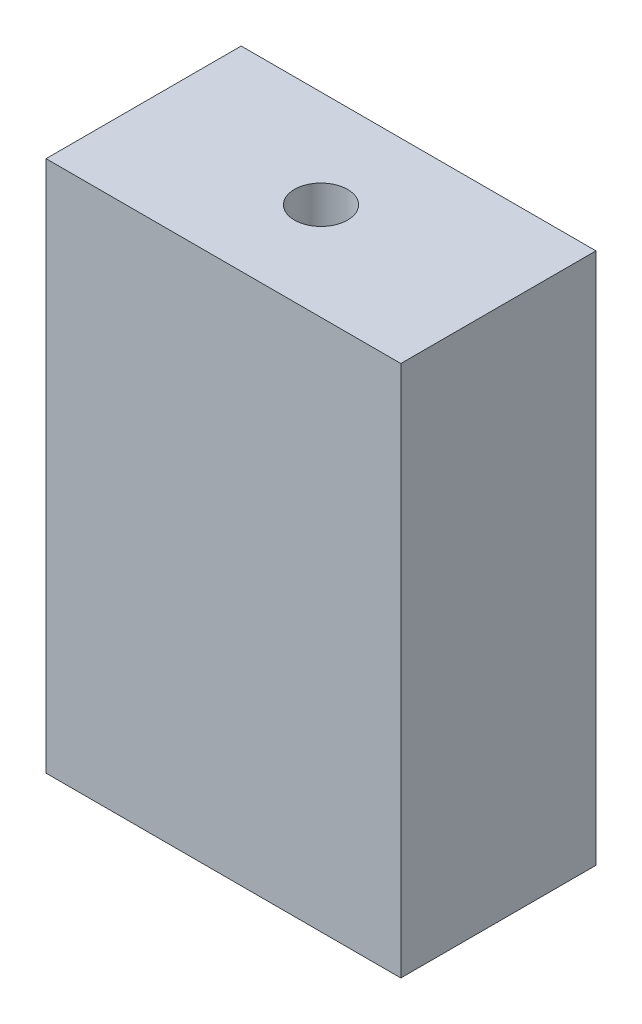
SolidWorks part; units mm, degrees
ref_plane "Front Plane" through (0, 0, 0) normal (0, 0, 1) x (1, 0, 0)
ref_plane "Top Plane" through (0, 0, 0) normal (0, 1, 0) x (1, 0, 0)
ref_plane "Right Plane" through (0, 0, 0) normal (1, 0, 0) x (0, 0, -1)
sketch "Sketch1" plane through (0, 0, 0) normal (0, 0, 1) x (1, 0, 0)
  line L1 (-10, 10) -> (10, 10)
  line L2 (-10, 10) -> (-10, -10)
  line L3 (-10, -10) -> (10, -10)
  line L4 (10, 10) -> (10, -10)
  circle A0 centre (0, 0) radius 8
  point P4 (0, 10)
  point P8 (-10, 0)
  dimension "D1" = 16
  dimension "D2" = 20
  dimension "D3" = 20
extrude "FirstLayer" add sketch "Sketch1" against normal blind 5
sketch "Sketch2" plane through (0, 0, 0) normal (0, 0, 1) x (1, 0, 0)
  line L4 (-10, 10) -> (-10, -10)
  line L5 (-10, -10) -> (10, -10)
  line L6 (10, -10) -> (10, 10)
  line L7 (10, 10) -> (-10, 10)
  line L8 (-10, 10) -> (-10, -10)
  line L9 (-10, -10) -> (10, -10)
  line L10 (10, -10) -> (10, 10)
  line L11 (10, 10) -> (-10, 10)
  circle A2 centre (0, 0) radius 6
  circle A3 centre (0, 0) radius 6
  dimension "D1" = 0
  dimension "D2" = 2
extrude "SecondLayer" add sketch "Sketch2" along normal blind 0.5
sketch "Sketch3" plane through (0, 0, 0.5) normal (0, 0, 1) x (1, 0, 0)
  line L4 (10, 10) -> (-10, 10)
  line L5 (-10, 10) -> (-10, -10)
  line L6 (-10, -10) -> (10, -10)
  line L7 (10, -10) -> (10, 10)
  line L8 (10, 10) -> (-10, 10)
  line L9 (-10, 10) -> (-10, -10)
  line L10 (-10, -10) -> (10, -10)
  line L11 (10, -10) -> (10, 10)
  dimension "D1" = 0
extrude "ThirdLayer" add sketch "Sketch3" along normal blind 5.5
sketch "Sketch4" plane through (0, 10, 0) normal (0, 1, 0) x (1, 0, 0)
  line L4 (-10, 5) -> (-10, -6)
  line L5 (-10, -6) -> (10, -6)
  line L6 (10, -6) -> (10, 5)
  line L7 (10, 5) -> (-10, 5)
  line L8 (-10, 5) -> (-10, -6)
  line L9 (-10, -6) -> (10, -6)
  line L10 (10, -6) -> (10, 5)
  line L11 (10, 5) -> (-10, 5)
  dimension "D1" = 0
extrude "Boss-Extrude4" add sketch "Sketch4" along normal blind 10
sketch "Sketch5" plane through (0, 20, 0) normal (0, 1, 0) x (1, 0, 0)
  line L0 (10, -0.5) -> (-10, -0.5) construction
  line L1 (10, -6) -> (10, 5) construction
  line L2 (-10, 5) -> (-10, -6) construction
  line L3 (0, -6) -> (0, 5) construction
  line L4 (-10, -6) -> (10, -6) construction
  line L5 (10, 5) -> (-10, 5) construction
  circle A0 centre (0, -0.5) radius 1.5 construction
  circle A1 centre (0, -0.5) radius 5 construction
  point P12 (0, -0.5)
  dimension "D1" = 3
  dimension "D2" = 10
ref_plane "Plane1" through (0, 10, 0) normal (0, 1, 0) x (1, 0, 0)
ref_plane "Plane2" through (0, 0, 0.5) normal (0, 0, -1) x (-1, 0, 0)
sketch "Sketch10" plane through (0, 0, 0.5) normal (0, 0, -1) x (-1, 0, 0)
  line L0 (0, 20) -> (0, 10) construction
  line L1 (-10, 20) -> (10, 20) construction
  line L2 (6.05, 10) -> (-6.05, 10) construction
  line L4 (-2.71, 12) -> (2.71, 12)
  line L5 (-2.71, 12) -> (-2.71, 14.36)
  line L6 (-2.71, 14.36) -> (2.71, 14.36)
  line L7 (2.71, 12) -> (2.71, 14.36)
  point P11 (0, 14.36)
  dimension "D1" = 5.42
  dimension "D2" = 2.36
  dimension "D3" = 8
extrude "Nut Hole" cut sketch "Sketch10" against normal blind 2.71 and the other way up to surface (5.5 mm away) other way up to face at (8, 0, -5)
sketch "Sketch11" plane through (0, 20, 0) normal (0, 1, 0) x (1, 0, 0)
  circle A0 centre (0, -0.5) radius 1.5
  dimension "D1" = 3
extrude "Screw Hole" cut sketch "Sketch11" against normal up to surface (5.64 mm away) up to face at (0, 14.36, -0.895)
